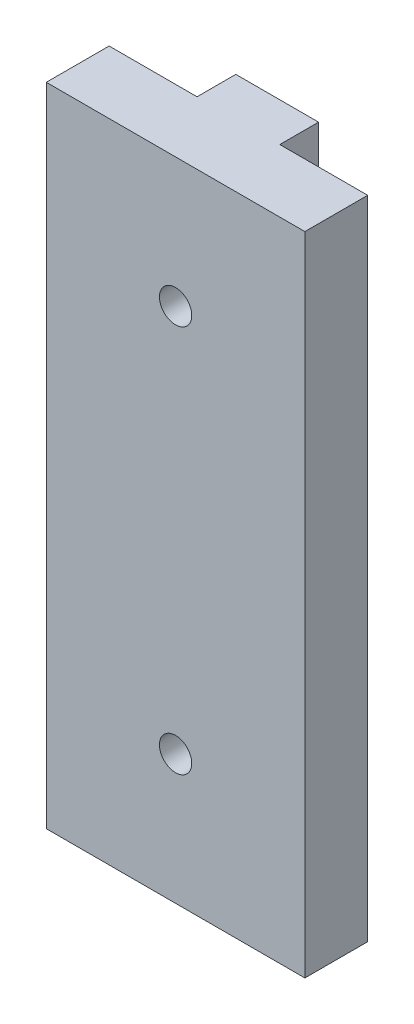
SolidWorks part; units mm, degrees
material "Nylon 101"
ref_plane "Front Plane" through (0, 0, 0) normal (0, 0, 1) x (1, 0, 0)
ref_plane "Top Plane" through (0, 0, 0) normal (0, 1, 0) x (1, 0, 0)
ref_plane "Right Plane" through (0, 0, 0) normal (1, 0, 0) x (0, 0, -1)
sketch "Sketch2" plane through (0, 0, 0) normal (0, 1, 0) x (1, 0, 0)
  line L0 (16.764, 6.1722) -> (25.4, 6.1722)
  line L1 (0, 0) -> (25.4, 0)
  line L2 (0, 0) -> (0, 6.1722)
  line L3 (0, 6.1722) -> (8.636, 6.1722)
  line L4 (25.4, 0) -> (25.4, 6.1722)
  line L6 (8.636, 6.1722) -> (8.636, 9.9822)
  line L7 (8.636, 9.9822) -> (16.764, 9.9822)
  line L8 (16.764, 6.1722) -> (16.764, 9.9822)
  dimension "D1" = 6.1722
  dimension "D2" = 8.128
  dimension "D3" = 25.4
  dimension "D4" = 8.636
  dimension "D5" = 3.81
extrude "Boss-Extrude1" add sketch "Sketch2" along normal blind 63.5
sketch "Sketch3" plane through (0, 0, 0) normal (0, 0, 1) x (1, 0, 0)
  line L0 (0, 63.5) -> (0, 0) construction
  line L1 (0, 63.5) -> (25.4, 63.5) construction
  circle A0 centre (12.7, 50.8) radius 1.5875
  circle A1 centre (12.7, 12.7) radius 1.5875
  dimension "D1" = 12.7
  dimension "D4" = 3.175
  dimension "D2" = 38.1
  dimension "D3" = 12.7
extrude "Cut-Extrude1" cut sketch "Sketch3" against normal blind 63.5
